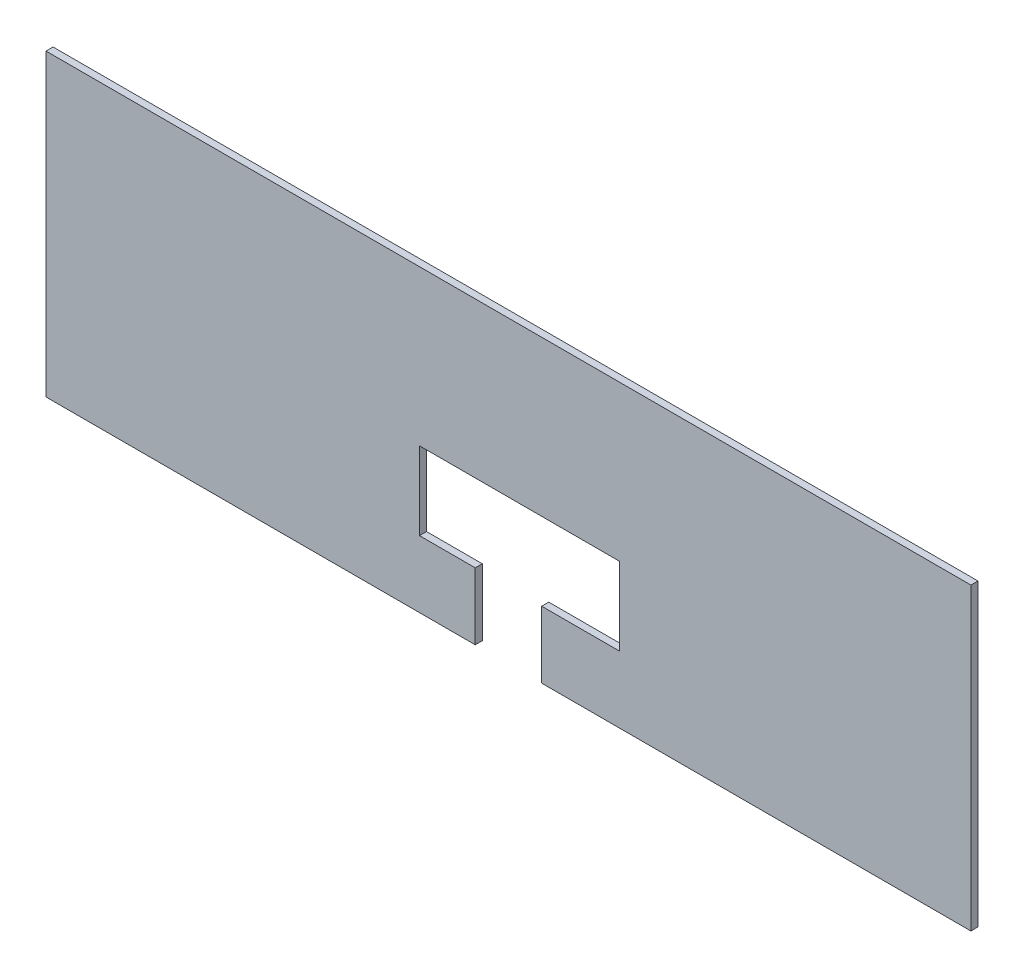
SolidWorks part; units mm, degrees
ref_plane "Front Plane" through (0, 0, 0) normal (0, 0, 1) x (1, 0, 0)
ref_plane "Top Plane" through (0, 0, 0) normal (0, 1, 0) x (1, 0, 0)
ref_plane "Right Plane" through (0, 0, 0) normal (1, 0, 0) x (0, 0, -1)
sketch "Sketch1" plane through (0, 0, 0) normal (0, 0, 1) x (1, 0, 0)
  line L1 (-368.4429, 111.1485) -> (47.6371, 111.1485)
  line L2 (-368.4429, 111.1485) -> (-368.4429, -23.6265)
  line L4 (47.6371, 111.1485) -> (47.6371, -23.6265)
  line L6 (-110.4529, 6.3735) -> (-110.4529, 41.3735)
  line L7 (-110.4529, 41.3735) -> (-200.4336, 41.3735)
  line L8 (-200.4336, 6.3735) -> (-200.4336, 41.3735)
  line L15 (17.6371, 6.3735) -> (-368.4429, 6.3735) construction
  line L16 (-175.3529, 6.3735) -> (-200.4336, 6.3735)
  line L17 (-145.4529, 6.3735) -> (-110.4529, 6.3735)
  line L18 (-145.4529, 6.3735) -> (-145.4529, -23.6265)
  line L19 (-175.3529, 6.3735) -> (-175.3529, -23.6265)
  line L21 (-141.4529, 41.3735) -> (-145.4529, 41.3735) construction
  line L22 (-368.4429, -23.6265) -> (-175.3529, -23.6265)
  line L23 (-145.4529, -23.6265) -> (47.6371, -23.6265)
  dimension "D1" = 89.9808
  dimension "D2" = 65
  dimension "D3" = 29.9
extrude "Boss-Extrude1" add sketch "Sketch1" along normal blind 3.175
